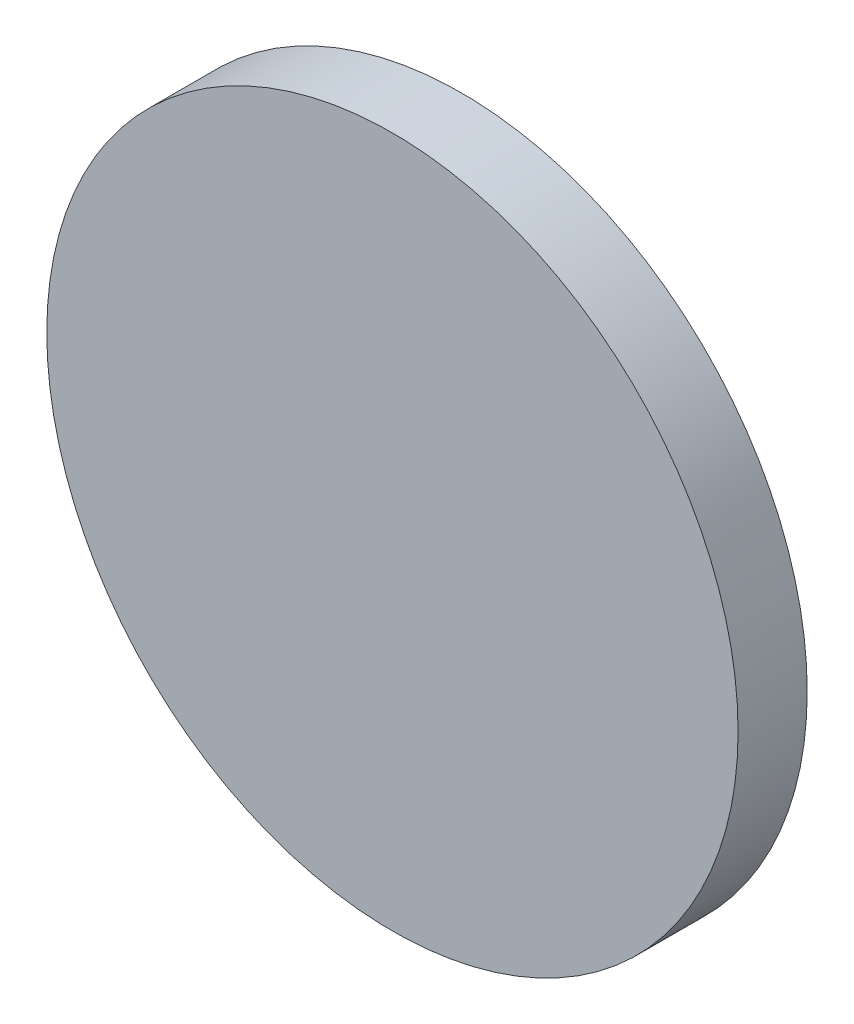
SolidWorks part; units mm, degrees
ref_plane "Front Plane" through (0, 0, 0) normal (0, 0, 1) x (1, 0, 0)
ref_plane "Top Plane" through (0, 0, 0) normal (0, 1, 0) x (1, 0, 0)
ref_plane "Right Plane" through (0, 0, 0) normal (1, 0, 0) x (0, 0, -1)
sketch "Sketch1" plane through (0, 0, 0) normal (0, 0, 1) x (1, 0, 0)
  circle A0 centre (0, 0) radius 15
  dimension "D1" = 30
extrude "Boss-Extrude1" add sketch "Sketch1" along normal blind 3
